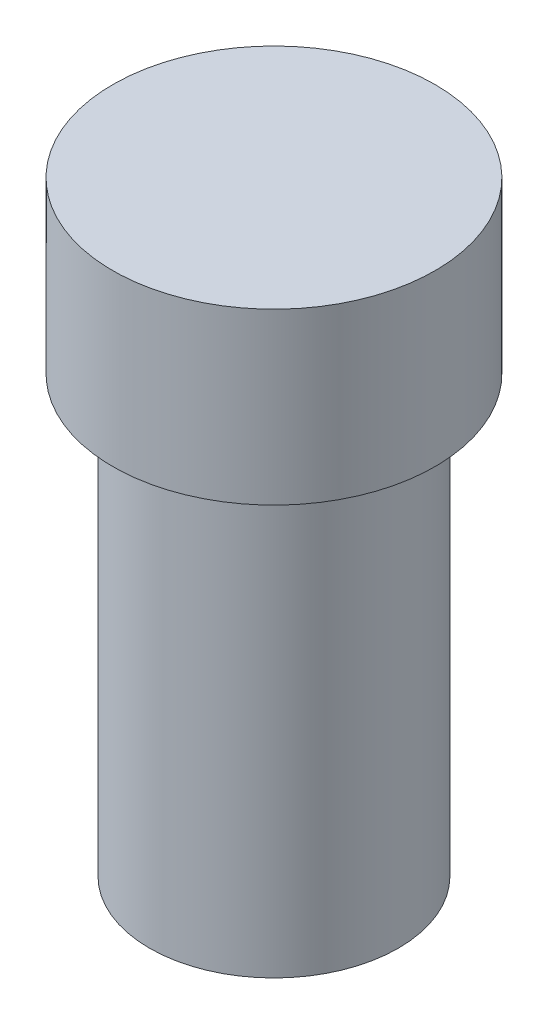
SolidWorks part; units mm, degrees
ref_plane "Front Plane" through (0, 0, 0) normal (0, 0, 1) x (1, 0, 0)
ref_plane "Top Plane" through (0, 0, 0) normal (0, 1, 0) x (1, 0, 0)
ref_plane "Right Plane" through (0, 0, 0) normal (1, 0, 0) x (0, 0, -1)
sketch "Sketch1" plane through (0, 0, 0) normal (0, 0, 1) x (1, 0, 0)
  line L0 (0, 0) -> (0, 120.5217) construction
  line L1 (0, 0) -> (22, 0)
  line L2 (22, 0) -> (22, 77)
  line L3 (22, 77) -> (28.5, 77)
  line L4 (28.5, 77) -> (28.5, 107)
  line L5 (28.5, 107) -> (0, 107)
  line L6 (0, 0) -> (0, 107)
  dimension "D1" = 77
  dimension "D2" = 30
  dimension "D3" = 57
  dimension "D4" = 44
revolve "Revolve1" add sketch "Sketch1" angle 360 about L0
fillet "Fillet1" radius 2 1 edges at (0, 77, -22)
